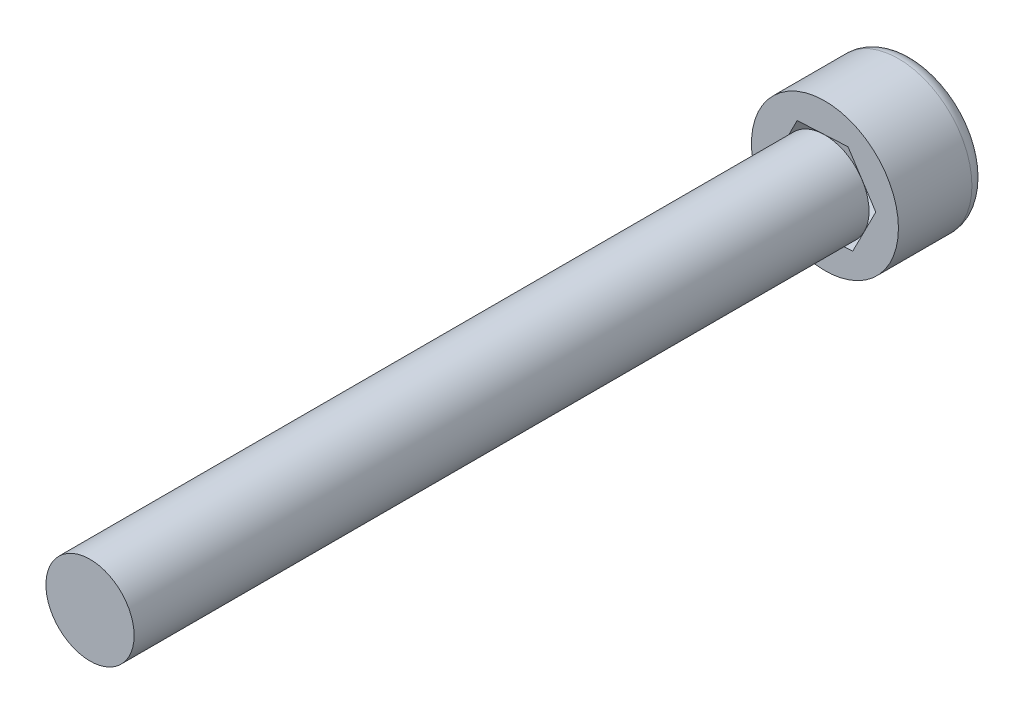
SolidWorks part; units mm, degrees
ref_plane "Front Plane" through (0, 0, 0) normal (0, 0, 1) x (1, 0, 0)
ref_plane "Top Plane" through (0, 0, 0) normal (0, 1, 0) x (1, 0, 0)
ref_plane "Right Plane" through (0, 0, 0) normal (1, 0, 0) x (0, 0, -1)
sketch "Sketch1" plane through (0, 0, 0) normal (0, 0, 1) x (1, 0, 0)
  circle A0 centre (0, 0) radius 2.5
  dimension "D1" = 5
extrude "Boss-Extrude1" add sketch "Sketch1" along normal blind 3
sketch "Sketch2" plane through (0, 0, 3) normal (0, 0, 1) x (1, 0, 0)
  circle A0 centre (0, 0) radius 1.5
  dimension "D1" = 3
extrude "Boss-Extrude2" add sketch "Sketch2" along normal blind 25
sketch "Sketch3" plane through (0, 0, 0) normal (0, 0, -1) x (-1, 0, 0)
  line L1 (0.7845, -1.5442) -> (1.7296, -0.0927)
  line L2 (1.7296, -0.0927) -> (0.9451, 1.4515)
  line L3 (0.9451, 1.4515) -> (-0.7845, 1.5442)
  line L4 (-0.7845, 1.5442) -> (-1.7296, 0.0927)
  line L5 (-1.7296, 0.0927) -> (-0.9451, -1.4515)
  line L6 (-0.9451, -1.4515) -> (0.7845, -1.5442)
  circle A0 centre (0, 0) radius 1.5 construction
  dimension "D1" = 3
extrude "Cut-Extrude1" cut sketch "Sketch3" against normal blind 3
fillet "Fillet1" radius 0.5 1 edges at (2.5, 0, 0)
